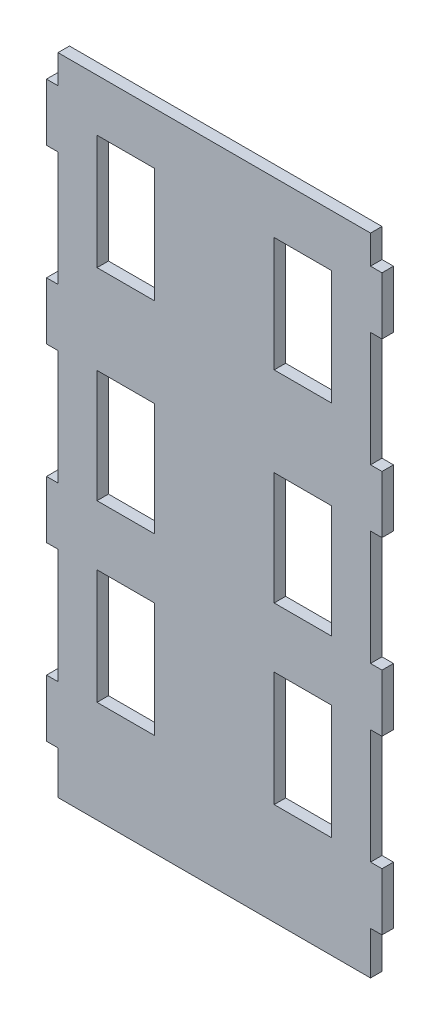
SolidWorks part; units mm, degrees
material "1060 Alloy"
ref_plane "Front Plane" through (0, 0, 0) normal (0, 0, 1) x (1, 0, 0)
ref_plane "Top Plane" through (0, 0, 0) normal (0, 1, 0) x (1, 0, 0)
ref_plane "Right Plane" through (0, 0, 0) normal (1, 0, 0) x (0, 0, -1)
sketch "Sketch1" plane through (0, 0, 0) normal (0, 0, 1) x (1, 0, 0)
  line L0 (66.8361, 121.1251) -> (-42.1639, 121.1251)
  line L1 (-42.1639, -103.8749) -> (66.8361, -103.8749)
  line L2 (-42.1639, 121.1251) -> (-42.1639, 111.1251)
  line L3 (-42.1639, 111.1251) -> (-46.1639, 111.1251)
  line L4 (-46.1639, 111.1251) -> (-46.1639, 91.1251)
  line L5 (-46.1639, 91.1251) -> (-42.1639, 91.1251)
  line L6 (-42.1639, 91.1251) -> (-42.1639, 51.1251)
  line L7 (-42.1639, 51.1251) -> (-46.1639, 51.1251)
  line L8 (-46.1639, 51.1251) -> (-46.1639, 31.1251)
  line L9 (-46.1639, 31.1251) -> (-42.1639, 31.1251)
  line L10 (-42.1639, 31.1251) -> (-42.1639, -8.8749)
  line L11 (-42.1639, -8.8749) -> (-46.1639, -8.8749)
  line L12 (-46.1639, -8.8749) -> (-46.1639, -28.8749)
  line L13 (-46.1639, -28.8749) -> (-42.1639, -28.8749)
  line L14 (-42.1639, -28.8749) -> (-42.1639, -68.8749)
  line L15 (-42.1639, -68.8749) -> (-46.1639, -68.8749)
  line L16 (-46.1639, -68.8749) -> (-46.1639, -88.8749)
  line L17 (-46.1639, -88.8749) -> (-42.1639, -88.8749)
  line L18 (-42.1639, -88.8749) -> (-42.1639, -103.8749)
  line L19 (12.3361, 121.1251) -> (12.3361, -103.8749) construction
  line L20 (66.8361, -88.8749) -> (66.8361, -103.8749)
  line L21 (70.8361, -88.8749) -> (66.8361, -88.8749)
  line L22 (70.8361, -68.8749) -> (70.8361, -88.8749)
  line L23 (66.8361, -68.8749) -> (70.8361, -68.8749)
  line L24 (66.8361, -28.8749) -> (66.8361, -68.8749)
  line L25 (70.8361, -28.8749) -> (66.8361, -28.8749)
  line L26 (70.8361, -8.8749) -> (70.8361, -28.8749)
  line L27 (66.8361, -8.8749) -> (70.8361, -8.8749)
  line L28 (66.8361, 31.1251) -> (66.8361, -8.8749)
  line L29 (70.8361, 31.1251) -> (66.8361, 31.1251)
  line L30 (70.8361, 51.1251) -> (70.8361, 31.1251)
  line L31 (66.8361, 51.1251) -> (70.8361, 51.1251)
  line L32 (66.8361, 91.1251) -> (66.8361, 51.1251)
  line L33 (70.8361, 91.1251) -> (66.8361, 91.1251)
  line L34 (70.8361, 111.1251) -> (70.8361, 91.1251)
  line L35 (66.8361, 111.1251) -> (70.8361, 111.1251)
  line L36 (66.8361, 121.1251) -> (66.8361, 111.1251)
  line L58 (53.2235, -68.3055) -> (33.2235, -68.3055)
  line L59 (-28.5513, 102.9902) -> (-8.5513, 102.9902)
  line L60 (-28.5513, 102.9902) -> (-28.5513, 62.9902)
  line L61 (-28.5513, 62.9902) -> (-8.5513, 62.9902)
  line L62 (-8.5513, 102.9902) -> (-8.5513, 62.9902)
  line L63 (-28.5513, 31.9485) -> (-8.5513, 31.9485)
  line L64 (-28.5513, 31.9485) -> (-28.5513, -7.4052)
  line L65 (-28.5513, -7.4052) -> (-8.5513, -7.4052)
  line L66 (-8.5513, 31.9485) -> (-8.5513, -7.4052)
  line L67 (-28.5513, -28.2766) -> (-8.5513, -28.2766)
  line L68 (-28.5513, -28.2766) -> (-28.5513, -68.3055)
  line L69 (-28.5513, -68.3055) -> (-8.5513, -68.3055)
  line L70 (-8.5513, -28.2766) -> (-8.5513, -68.3055)
  line L71 (33.2235, -28.2766) -> (33.2235, -68.3055)
  line L72 (53.2235, -28.2766) -> (33.2235, -28.2766)
  line L73 (53.2235, -28.2766) -> (53.2235, -68.3055)
  line L74 (53.2235, -7.4052) -> (33.2235, -7.4052)
  line L75 (33.2235, 31.9485) -> (33.2235, -7.4052)
  line L76 (53.2235, 31.9485) -> (33.2235, 31.9485)
  line L77 (53.2235, 31.9485) -> (53.2235, -7.4052)
  line L78 (53.2235, 62.9902) -> (33.2235, 62.9902)
  line L79 (33.2235, 102.9902) -> (33.2235, 62.9902)
  line L80 (53.2235, 102.9902) -> (33.2235, 102.9902)
  line L81 (53.2235, 102.9902) -> (53.2235, 62.9902)
  dimension "D1" = 4
  dimension "D2" = 20
  dimension "D3" = 40
  dimension "D4" = 109
  dimension "D5" = 10
  dimension "D6" = 225
  dimension "D13" = 109
extrude "Boss-Extrude1" add sketch "Sketch1" along normal blind 4
